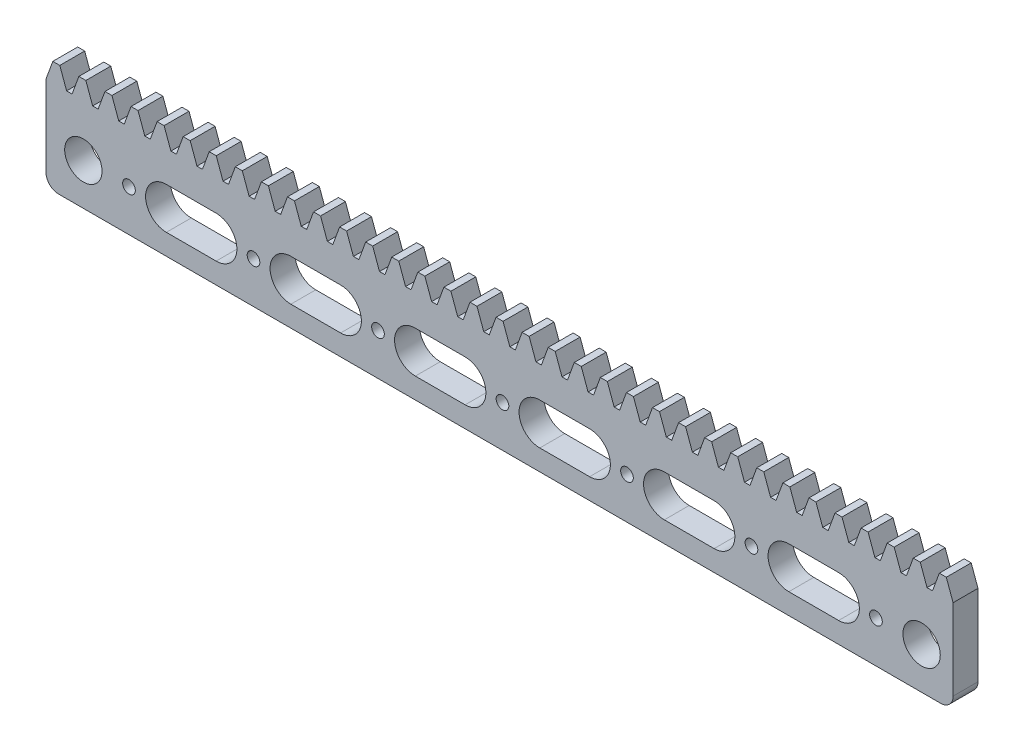
SolidWorks part; units mm, degrees
material "POM Acetal Coopolymer聚甲醛树脂"
ref_plane "前视基准面" through (0, 0, 0) normal (0, 0, 1) x (1, 0, 0)
ref_plane "上视基准面" through (0, 0, 0) normal (0, 1, 0) x (1, 0, 0)
ref_plane "右视基准面" through (0, 0, 0) normal (1, 0, 0) x (0, 0, -1)
sketch "草图1" plane through (0, 0, 0) normal (0, 0, 1) x (1, 0, 0)
  line L1 (0, 0) -> (218.5897, 0)
  line L2 (0, 0) -> (0, -22.5)
  line L3 (0, -22.5) -> (218.5897, -22.5)
  line L4 (218.5897, 0) -> (218.5897, -22.5)
  dimension "D1" = 22.5
  dimension "L" = 218.5897
extrude "拉伸1" add sketch "草图1" along normal blind 6
sketch "草图2" plane through (0, 0, 6) normal (0, 0, 1) x (1, 0, 0)
  line L0 (0, 0) -> (1.6379, 4.5)
  line L1 (1.6379, 4.5) -> (3.3236, 4.5)
  line L2 (3.3236, 4.5) -> (4.9614, 0)
  line L3 (218.5897, 0) -> (0, 0) construction
  line L4 (0, 0) -> (4.9614, 0)
  line L5 (0.9099, 2.5) -> (4.0515, 2.5) construction
  dimension "D2" = 70
  dimension "alpha" = 110
  dimension "ha" = 2
  dimension "hf" = 2.5
  dimension "S" = 3.1416
extrude "拉伸2" add sketch "草图2" against normal up to surface (6 mm away) up to face at (109.2949, -11.25, 0)
pattern_linear "阵列(线性)1" count 35 spacing 6.2832 along (1, 0, 0) of "拉伸2"
sketch "草图3" plane through (0, 0, 6) normal (0, 0, 1) x (1, 0, 0)
  line L2 (0, -22.5) -> (218.5897, -22.5) construction
  line L3 (0, 0) -> (0, -22.5) construction
  circle A0 centre (20, -12.5) radius 1.525
  dimension "D3" = 3.05
  dimension "D1" = 10
  dimension "D2" = 20
extrude "切除-拉伸1" cut sketch "草图3" against normal blind 10
pattern_linear "阵列(线性)2" count 7 spacing 30 along (1, 0, 0) of "切除-拉伸1"
fillet "圆角1" radius 3 2 edges at (218.5897, -22.5, 3) (0, -22.5, 3)
sketch "草图4" plane through (0, 0, 6) normal (0, 0, 1) x (1, 0, 0)
  line L0 (9, -12.5) -> (20, -12.5) construction
  line L1 (0, 0) -> (0, -19.5) construction
  line L2 (29, -12.5) -> (41, -12.5) construction
  line L3 (29, -7.5) -> (41, -7.5)
  line L4 (29, -17.5) -> (41, -17.5)
  line L5 (50, -12.5) -> (50, -32.3207) construction
  line L6 (71, -12.5) -> (59, -12.5) construction
  line L7 (71, -7.5) -> (59, -7.5)
  line L8 (71, -17.5) -> (59, -17.5)
  line L9 (80, -12.5) -> (80, -32.3207) construction
  line L10 (89, -12.5) -> (101, -12.5) construction
  line L11 (89, -7.5) -> (101, -7.5)
  line L12 (89, -17.5) -> (101, -17.5)
  line L13 (110, -12.5) -> (110, -32.3207) construction
  line L14 (191, -12.5) -> (179, -12.5) construction
  line L15 (191, -7.5) -> (179, -7.5)
  line L16 (191, -17.5) -> (179, -17.5)
  line L17 (149, -12.5) -> (161, -12.5) construction
  line L18 (149, -7.5) -> (161, -7.5)
  line L19 (149, -17.5) -> (161, -17.5)
  line L20 (131, -12.5) -> (119, -12.5) construction
  line L21 (131, -7.5) -> (119, -7.5)
  line L22 (131, -17.5) -> (119, -17.5)
  line L23 (140, -12.5) -> (140, -32.3207) construction
  line L24 (170, -12.5) -> (170, -32.3207) construction
  line L25 (211, -12.5) -> (200, -12.5) construction
  circle A0 centre (9, -12.5) radius 4.5
  arc A1 (29, -7.5) -> (29, -17.5) centre (29, -12.5) ccw
  arc A2 (41, -17.5) -> (41, -7.5) centre (41, -12.5) ccw
  circle A3 centre (50, -12.5) radius 1.525 construction
  circle A4 centre (20, -12.5) radius 1.525 construction
  arc A5 (71, -7.5) -> (71, -17.5) centre (71, -12.5) cw
  arc A6 (59, -17.5) -> (59, -7.5) centre (59, -12.5) cw
  arc A7 (89, -7.5) -> (89, -17.5) centre (89, -12.5) ccw
  arc A8 (101, -17.5) -> (101, -7.5) centre (101, -12.5) ccw
  arc A9 (191, -7.5) -> (191, -17.5) centre (191, -12.5) cw
  arc A10 (179, -17.5) -> (179, -7.5) centre (179, -12.5) cw
  arc A11 (149, -7.5) -> (149, -17.5) centre (149, -12.5) ccw
  arc A12 (161, -17.5) -> (161, -7.5) centre (161, -12.5) ccw
  arc A13 (131, -7.5) -> (131, -17.5) centre (131, -12.5) cw
  arc A14 (119, -17.5) -> (119, -7.5) centre (119, -12.5) cw
  circle A15 centre (211, -12.5) radius 4.5
  point P8 (35, -12.5)
  point P22 (65, -12.5)
  point P32 (95, -12.5)
  point P42 (185, -12.5)
  point P49 (155, -12.5)
  point P56 (125, -12.5)
  dimension "D2" = 9
  dimension "D3" = 5
  dimension "D1" = 9
  dimension "D4" = 9
  dimension "D5" = 9
extrude "切除-拉伸2" cut sketch "草图4" against normal blind 10
equation "\"d\"=\"S@草图2\" * 2"
equation "\"z\"= int(  \"L@草图1\" / (  \"S@草图2\" * 2 ) + 0.5 )"
equation "\"D5@草图4\"=\"D4@草图4\""
